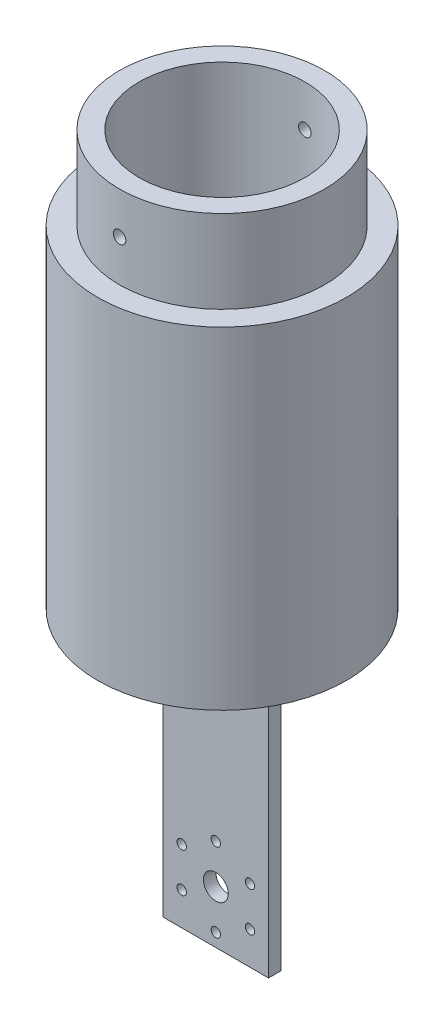
SolidWorks part; units mm, degrees
ref_plane "Front Plane" through (0, 0, 0) normal (0, 0, 1) x (1, 0, 0)
ref_plane "Top Plane" through (0, 0, 0) normal (0, 1, 0) x (1, 0, 0)
ref_plane "Right Plane" through (0, 0, 0) normal (1, 0, 0) x (0, 0, -1)
sketch "Sketch2" plane through (0, 0, 0) normal (0, 1, 0) x (1, 0, 0)
  line L0 (0, 0) -> (25.4, 0)
  line L1 (25.4, 0) -> (25.4, 3)
  line L2 (25.4, 3) -> (0, 3)
  line L3 (0, 3) -> (0, 0)
  dimension "D2" = 3
  dimension "D1" = 25.4
extrude "Boss-Extrude1" add sketch "Sketch2" along normal blind 70
sketch "Sketch3" plane through (0, 0, 0) normal (0, 0, 1) x (1, 0, 0)
  line L0 (0, 0) -> (12.7, 0) construction
  line L1 (0, 0) -> (25.4, 0) construction
  line L2 (12.7, 0) -> (12.7, 12.7) construction
  circle A0 centre (12.7, 12.7) radius 3
  circle A2 centre (12.7, 22.2) radius 1.4
  circle A3 centre (20.9272, 17.45) radius 1.4
  circle A4 centre (20.9272, 7.95) radius 1.4
  circle A5 centre (12.7, 3.2) radius 1.4
  circle A6 centre (4.4728, 7.95) radius 1.4
  circle A7 centre (4.4728, 17.45) radius 1.4
  point P23 (12.7, 12.7)
  dimension "D2" = 6
  dimension "D4" = 2.8
  dimension "D1" = 12.7
  dimension "D5" = 6
sketch "Sketch4" plane through (0, 70, 0) normal (0, 1, 0) x (1, 0, 0)
  circle A0 centre (12.7, 1.5) radius 30
  dimension "D1" = 60
extrude "Boss-Extrude2" add sketch "Sketch4" along normal blind 10
sketch "Sketch5" plane through (0, 80, 0) normal (0, 1, 0) x (1, 0, 0)
  circle A0 centre (12.7, 1.5) radius 30
  circle A1 centre (12.7, 1.5) radius 20
  dimension "D1" = 40
extrude "Boss-Extrude3" add sketch "Sketch5" along normal blind 70
sketch "Sketch8" plane through (0, 150, 0) normal (0, 1, 0) x (1, 0, 0)
  circle A0 centre (12.7, 1.5) radius 24.75
  circle A1 centre (12.7, 1.5) radius 20
  dimension "D1" = 49.5
extrude "Boss-Extrude4" add sketch "Sketch8" along normal blind 20
sketch "Sketch9" plane through (0, 0, 0) normal (0, 0, 1) x (1, 0, 0)
  line L0 (12.7, 170) -> (12.7, 160) construction
  line L1 (37.45, 170) -> (-12.05, 170) construction
  circle A0 centre (12.7, 160) radius 1.5
  dimension "D2" = 3
  dimension "D1" = 10
extrude "Cut-Extrude4" cut sketch "Sketch9" against normal through all and the other way through all
hole_wizard "#4-40 Tapped Hole1" positions "Sketch11" profile "Sketch10" tap size "#4-40" standard "ANSI Inch"
sketch "Sketch11" plane through (0, 0, 0) normal (0, 0, 1) x (1, 0, 0)
  point P0 (12.7, 22.2)
  point P3 (20.9272, 17.45)
  point P6 (20.9272, 7.95)
  point P9 (12.7, 3.2)
  point P12 (4.4728, 7.95)
  point P15 (4.4728, 17.45)
sketch "Sketch10" plane through (12.7, 22.2, 0) normal (1, 0, 0) x (0, -1, 0)
  line L0 (0, 0) -> (0, 8.2792)
  line L1 (0, 8.2792) -> (1.1303, 7.6)
  line L2 (1.1303, 7.6) -> (1.1303, 0)
  line L5 (1.1303, 0) -> (0, 0)
  line L10 (0, 8.2792) -> (-1.1303, 7.6) construction
  line L11 (0, -6.35) -> (0, 107.95) construction
  dimension "Tap Drill Dia." = 2.2606
  dimension "Tap Drill Depth" = 7.6
  dimension "Drill Angle" = 118
cosmetic thread "Hole Thread1" parameters "D1"=3, "D2"=2.8448
cosmetic thread "Hole Thread2" parameters "D1"=3, "D2"=2.8448
cosmetic thread "Hole Thread3" parameters "D1"=3, "D2"=2.8448
cosmetic thread "Hole Thread4" parameters "D1"=3, "D2"=2.8448
cosmetic thread "Hole Thread5" parameters "D1"=3, "D2"=2.8448
cosmetic thread "Hole Thread6" parameters "D1"=3, "D2"=2.8448
extrude "Cut-Extrude5" cut sketch "Sketch3" against normal blind 10 contours A0
sketch "Sketch12" plane through (0, 80, 0) normal (0, 1, 0) x (1, 0, 0)
  circle A0 centre (12.7, 1.5) radius 27
  circle A1 centre (12.7, 1.5) radius 20
  dimension "D1" = 54
extrude "Cut-Extrude6" cut sketch "Sketch12" along normal blind 60
